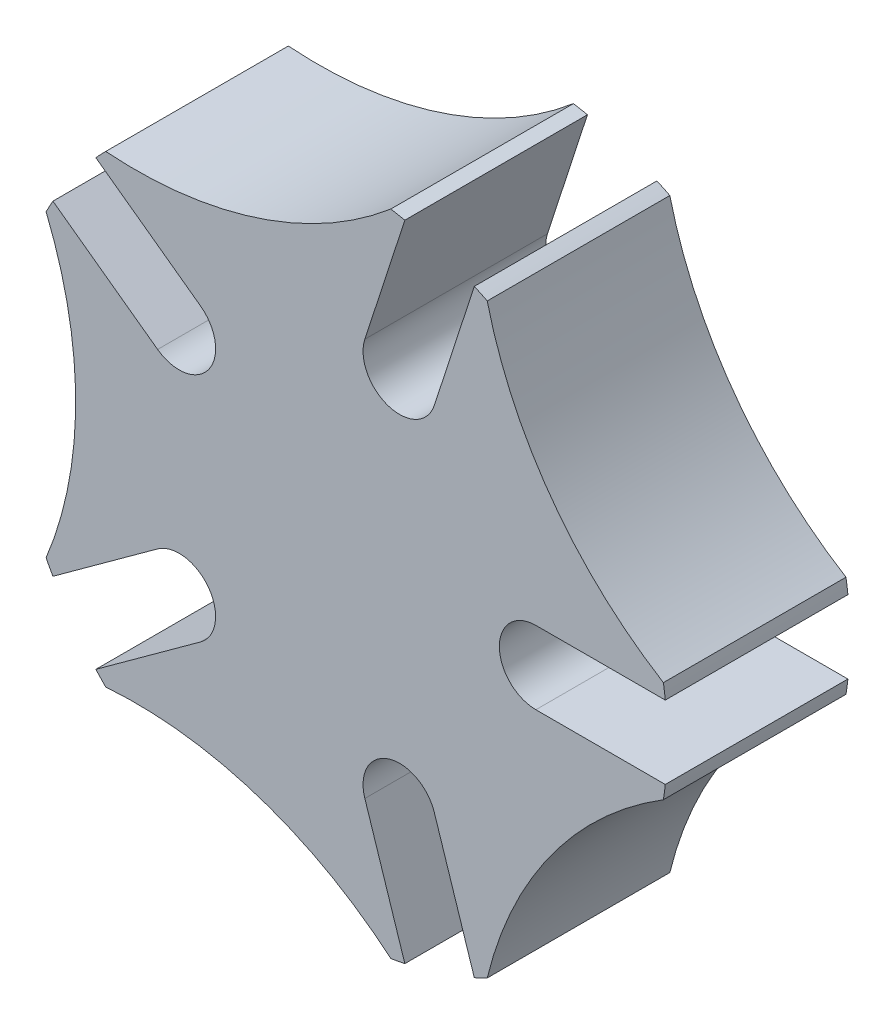
SolidWorks part; units mm, degrees
ref_plane "Front Plane" through (0, 0, 0) normal (0, 0, 1) x (1, 0, 0)
ref_plane "Top Plane" through (0, 0, 0) normal (0, 1, 0) x (1, 0, 0)
ref_plane "Right Plane" through (0, 0, 0) normal (1, 0, 0) x (0, 0, -1)
sketch "Croquis1" plane through (0, 0, 0) normal (0, 0, 1) x (1, 0, 0)
  line L0 (0, 0) -> (-13.2391, 9.6188) construction
  line L1 (0, 0) -> (-18, 0) construction
  line L2 (0, 0) -> (-16.0176, -11.6374) construction
  line L3 (0, 0) -> (-4.3687, 3.174)
  line L4 (-4.3687, 3.174) -> (-10.4255, 7.5745) construction
  line L5 (-4.9565, 2.365) -> (-11.0132, 6.7655)
  line L6 (-3.7809, 3.9831) -> (-9.8377, 8.3836)
  line L7 (-18, 0) -> (-10.4255, 7.5745) construction
  line L8 (1.6687, 5.1357) -> (3.9822, 12.2559) construction
  line L9 (0.7176, 5.4447) -> (3.0311, 12.5649)
  line L10 (2.6197, 4.8267) -> (4.9332, 11.9468)
  line L11 (5.4, 0) -> (12.8866, 0) construction
  line L12 (5.4, 1) -> (12.8866, 1)
  line L13 (5.4, -1) -> (12.8866, -1)
  line L14 (1.6687, -5.1357) -> (3.9822, -12.2559) construction
  line L17 (2.6197, -4.8267) -> (4.9332, -11.9468)
  line L20 (0.7176, -5.4447) -> (3.0311, -12.5649)
  line L21 (-4.3687, -3.174) -> (-10.4255, -7.5745) construction
  line L22 (-3.7809, -3.9831) -> (-9.8377, -8.3836)
  line L23 (-4.9565, -2.365) -> (-11.0132, -6.7655)
  circle A0 centre (0, 0) radius 8.9995
  circle A7 centre (-18, 0) radius 10.8
  arc A8 (-4.9565, 2.365) -> (-3.7809, 3.9831) centre (-4.3687, 3.174) ccw
  arc A9 (-9.8377, 8.3836) -> (-11.0132, 6.7655) centre (-10.4255, 7.5745) ccw
  circle A10 centre (-5.5623, 17.119) radius 10.8
  arc A11 (0.7176, 5.4447) -> (2.6197, 4.8267) centre (1.6687, 5.1357) ccw
  arc A12 (4.9332, 11.9468) -> (3.0311, 12.5649) centre (3.9822, 12.2559) ccw
  circle A13 centre (14.5623, 10.5801) radius 10.8
  arc A14 (5.4, 1) -> (5.4, -1) centre (5.4, 0) ccw
  arc A15 (12.8866, -1) -> (12.8866, 1) centre (12.8866, 0) ccw
  circle A22 centre (14.5623, -10.5801) radius 10.8
  arc A23 (2.6197, -4.8267) -> (0.7176, -5.4447) centre (1.6687, -5.1357) ccw
  arc A24 (3.0311, -12.5649) -> (4.9332, -11.9468) centre (3.9822, -12.2559) ccw
  circle A25 centre (-5.5623, -17.119) radius 10.8
  arc A26 (-3.7809, -3.9831) -> (-4.9565, -2.365) centre (-4.3687, -3.174) ccw
  arc A27 (-11.0132, -6.7655) -> (-9.8377, -8.3836) centre (-10.4255, -7.5745) ccw
  point P4 (-7.3971, 5.3743)
  point P14 (2.8254, -8.6958)
  point P15 (0, 0)
  point P18 (-7.2807, 5.2897)
  point P20 (2.8254, 8.6958)
  point P29 (9.1433, 0)
  point P44 (-7.3971, -5.3743)
  point P47 (0, 0)
  dimension "D3" = 17.9989
  dimension "D4" = 21.6
  dimension "D8" = 1
  dimension "D1" = 18
  dimension "D2" = 36
  dimension "D5" = 72
  dimension "D6" = 19.7988
  dimension "D7" = 5.4
  dimension "D9" = 45
  dimension "D10" = 5
extrude "Saliente-Extruir1" add sketch "Croquis1" along normal blind 5
equation "\"S\"= \"d\" * 0.3"
equation "\"R\"= \"d\" * cos ( \"Bo\" * pi / 360 )"
equation "\"n\"= 5"
equation "\"Bo\"= 360 / \"n\""
equation "\"din\"= \"d\" / 10"
equation "\"d\"=18"
equation "\"D4@Croquis1\"=\"d\"*1.2"
equation "\"D1@Croquis1\"=\"d\""
equation "\"D2@Croquis1\"=\"Bo\"/2"
equation "\"D5@Croquis1\"=\"Bo\""
equation "\"D6@Croquis1\"=\"R\"*1.1"
equation "\"D7@Croquis1\"=\"S\""
equation "\"R1\"=1"
equation "\"D8@Croquis1\"=\"R1\""
equation "\"a\"= 12.7323"
equation "\"D3@Croquis1\"=\"R\""
equation "\"ancho\"=5"
equation "\"D1@Saliente-Extruir1\"=\"ancho\""
equation "\"D10@Croquis1\"=\"n\""
